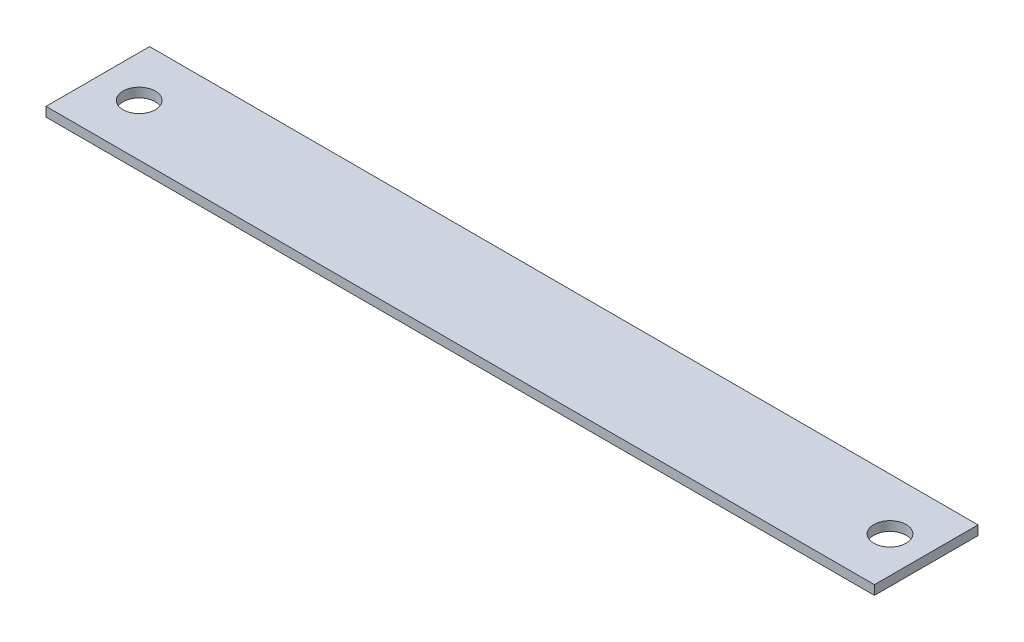
SolidWorks part; units mm, degrees
ref_plane "Front Plane" through (0, 0, 0) normal (0, 0, 1) x (1, 0, 0)
ref_plane "Top Plane" through (0, 0, 0) normal (0, 1, 0) x (1, 0, 0)
ref_plane "Right Plane" through (0, 0, 0) normal (1, 0, 0) x (0, 0, -1)
sketch "Sketch1" plane through (0, 0, 0) normal (0, 1, 0) x (1, 0, 0)
  line L1 (0, 0) -> (203.2, 0)
  line L2 (0, 0) -> (0, 25.4)
  line L3 (0, 25.4) -> (203.2, 25.4)
  line L4 (203.2, 0) -> (203.2, 25.4)
  dimension "D1" = 203.2
  dimension "D2" = 25.4
extrude "Boss-Extrude1" add sketch "Sketch1" along normal blind 2.286
sketch "Sketch2" plane through (0, 2.286, 0) normal (0, 1, 0) x (1, 0, 0)
  line L0 (0, 25.4) -> (0, 0) construction
  circle A0 centre (10.16, 12.7) radius 3.9688
  circle A1 centre (194.31, 12.7) radius 3.9687
  point P8 (0, 12.7)
  dimension "D1" = 7.9375
  dimension "D2" = 10.16
  dimension "D3" = 184.15
  dimension "D4" = 7.9375
extrude "Cut-Extrude1" cut sketch "Sketch2" against normal through all
